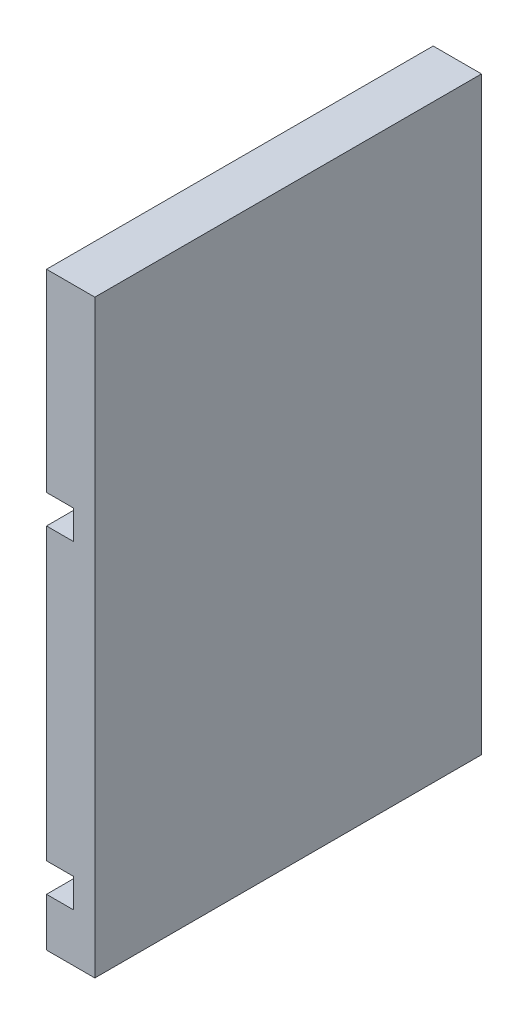
SolidWorks part; units mm, degrees
ref_plane "Plan de face" through (0, 0, 0) normal (0, 0, 1) x (1, 0, 0)
ref_plane "Plan de dessus" through (0, 0, 0) normal (0, 1, 0) x (1, 0, 0)
ref_plane "Plan de droite" through (0, 0, 0) normal (1, 0, 0) x (0, 0, -1)
sketch "Esquisse1" plane through (0, 0, 0) normal (0, 0, 1) x (1, 0, 0)
  line L1 (0, 53) -> (5, 53)
  line L2 (5, 53) -> (5, -8)
  line L3 (5, -8) -> (0, -8)
  line L4 (0, -8) -> (0, -3)
  line L5 (0, -3) -> (2.7876, -3)
  line L6 (2.7876, -3) -> (2.7876, 0)
  line L7 (2.7876, 0) -> (0, 0)
  line L8 (0, 53) -> (0, 33)
  line L9 (0, 33) -> (2.7876, 33)
  line L10 (2.7876, 33) -> (2.7876, 30)
  line L11 (2.7876, 30) -> (0, 30)
  line L12 (0, 30) -> (0, 0)
  dimension "D1" = 30
  dimension "D2" = 20
  dimension "D3" = 5
  dimension "D4" = 5
  dimension "D5" = 3
  dimension "D6" = 3
extrude "Boss.-Extru.1" add sketch "Esquisse1" along normal blind 40
